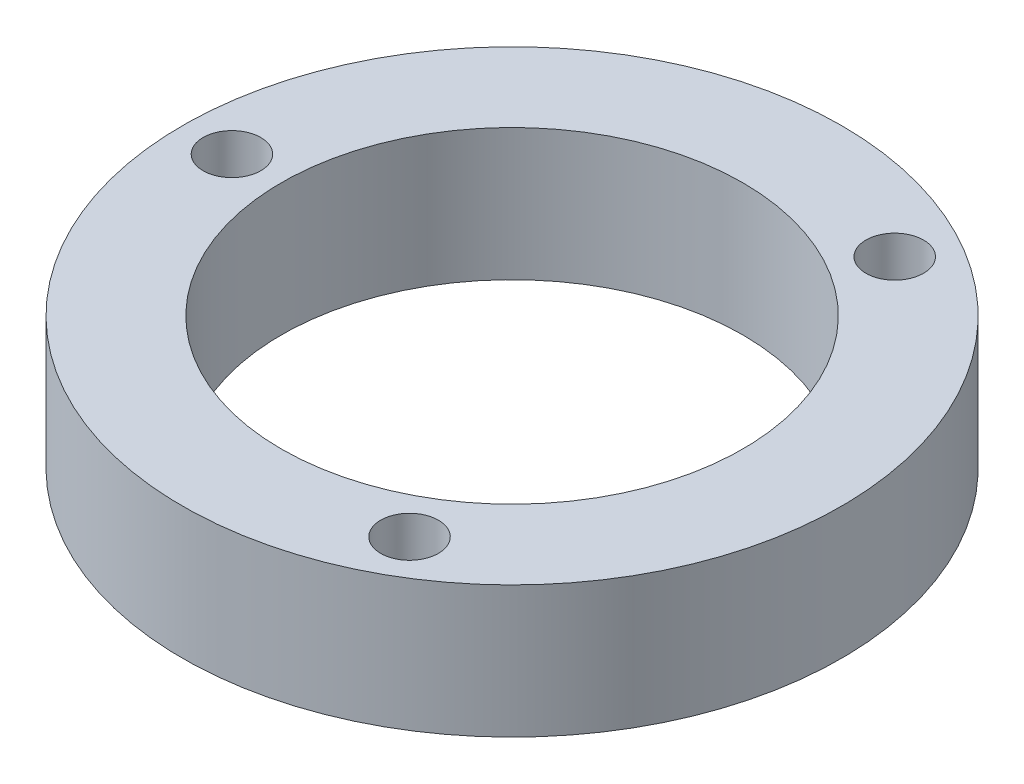
SolidWorks part; units mm, degrees
ref_plane "Front Plane" through (0, 0, 0) normal (0, 0, 1) x (1, 0, 0)
ref_plane "Top Plane" through (0, 0, 0) normal (0, 1, 0) x (1, 0, 0)
ref_plane "Right Plane" through (0, 0, 0) normal (1, 0, 0) x (0, 0, -1)
sketch "Sketch1" plane through (0, 0, 0) normal (0, -1, 0) x (1, 0, 0)
  circle A0 centre (-34.1432, 5.1297) radius 20
  dimension "D1" = 40
extrude "Boss-Extrude1" add sketch "Sketch1" along normal blind 8
sketch "Sketch2" plane through (0, 0, 0) normal (0, 1, 0) x (1, 0, 0)
  circle A0 centre (-34.1432, -5.1297) radius 14
  dimension "D1" = 28
extrude "Cut-Extrude1" cut sketch "Sketch2" against normal blind 8
sketch "Sketch3" plane through (0, -8, 0) normal (0, -1, 0) x (1, 0, 0)
  circle A0 centre (-25.6432, 19.8521) radius 1.75
  circle A1 centre (-25.6432, -9.5927) radius 1.75
  circle A2 centre (-51.1432, 5.1297) radius 1.75
extrude "Cut-Extrude2" cut sketch "Sketch3" against normal up to next
